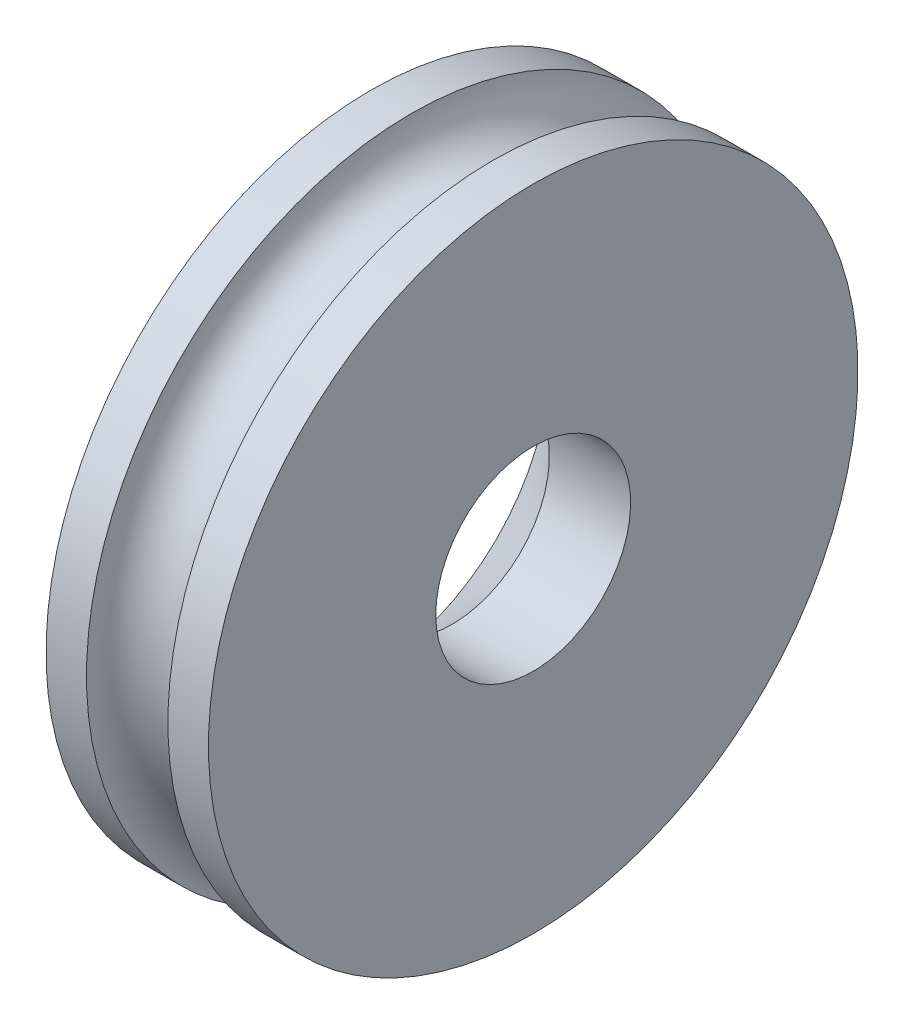
SolidWorks part; units mm, degrees
ref_plane "Ebene vorne" through (0, 0, 0) normal (0, 0, 1) x (1, 0, 0)
ref_plane "Ebene oben" through (0, 0, 0) normal (0, 1, 0) x (1, 0, 0)
ref_plane "Ebene rechts" through (0, 0, 0) normal (1, 0, 0) x (0, 0, -1)
sketch "Skizze1" plane through (0, 0, 0) normal (0, 0, 1) x (1, 0, 0)
  line L0 (0, 0) -> (0, 4)
  line L1 (0, 0) -> (-2, 0)
  line L2 (-2, 0) -> (-2, 4)
  line L3 (-2, 4) -> (-1.502, 4)
  line L4 (0, 4) -> (-0.4993, 4)
  arc A1 (-0.4993, 4) -> (-1.502, 4) centre (-1.0007, 4) cw
revolve "Rotation1" add sketch "Skizze1" angle 360 about L1
hole_wizard "Formsenkung für M2 Linsensenkschraube mit Schlitz1" positions "Skizze2" profile "Skizze3" countersink size "M2" standard "ISO"
sketch "Skizze2" plane through (-2, 0, 0) normal (-1, 0, 0) x (0, 0, 1)
  point P0 (0, 0)
sketch "Skizze3" plane through (-2, 0, 0) normal (0, 1, 0) x (0, 0, 1)
  line L0 (0, 0) -> (0, 5.721)
  line L1 (0, 5.721) -> (1.2, 5)
  line L2 (1.2, 5) -> (1.2, 1)
  line L3 (1.2, 1) -> (2.2, 0)
  line L5 (2.2, 0) -> (0, 0)
  line L6 (-1.2, 1) -> (-2.2, 0) construction
  line L10 (0, 5.721) -> (-1.2, 5) construction
  line L11 (0, -6.35) -> (0, 107.95) construction
  dimension "Bohrerdurchmesser" = 2.4
  dimension "Bohrungstiefe" = 5
  dimension "Senkdurchmesser (Oben)" = 4.4
  dimension "Senkwinkel (Oben)" = 90
  dimension "Spitzenwinkel" = 118
